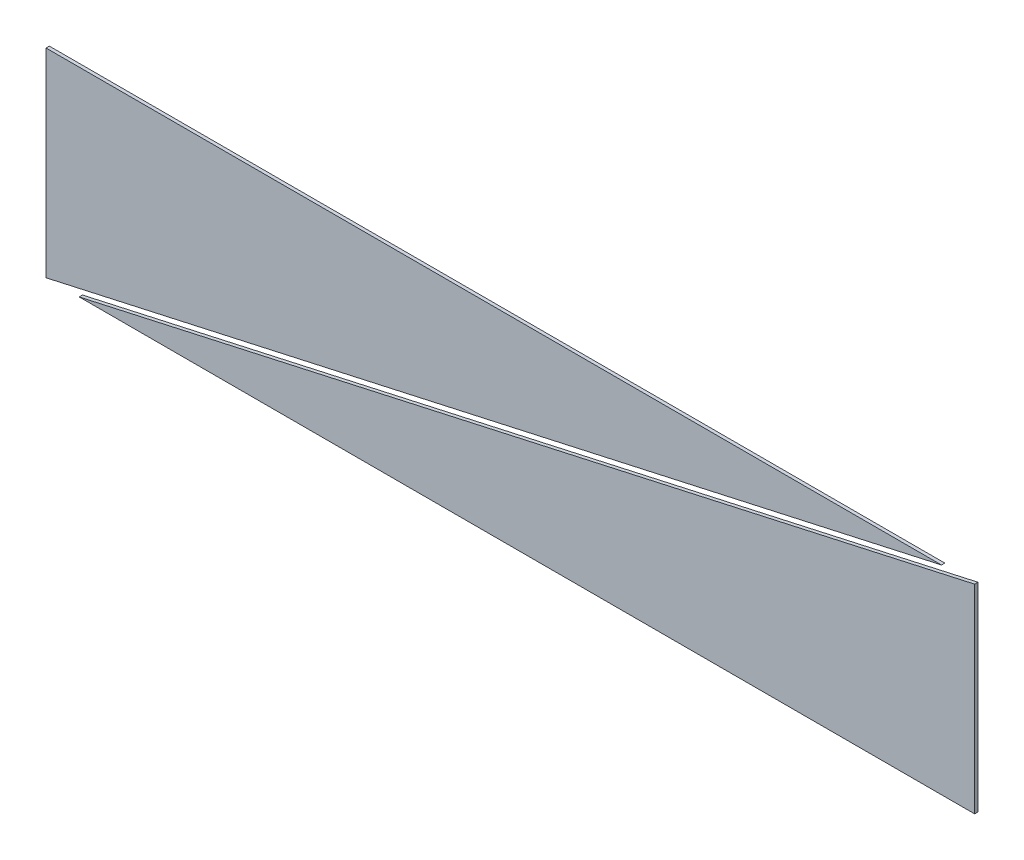
SolidWorks part; units mm, degrees
ref_plane "Front Plane" through (0, 0, 0) normal (0, 0, 1) x (1, 0, 0)
ref_plane "Top Plane" through (0, 0, 0) normal (0, 1, 0) x (1, 0, 0)
ref_plane "Right Plane" through (0, 0, 0) normal (1, 0, 0) x (0, 0, -1)
sketch "Sketch11" plane through (0, -5, 0) normal (0, 0, 1) x (1, 0, 0)
  line L0 (-35, 12.5) -> (32.5, 12.5)
  line L1 (-35, 12.5) -> (-35, -2.5)
  line L2 (-32.5, -2.5) -> (35, -2.5)
  line L3 (35, -2.5) -> (35, 12.5)
  line L5 (32.5, 12.5) -> (-35, -2.5)
  line L6 (35, 12.5) -> (-32.5, -2.5)
extrude "Boss-Extrude1" add sketch "Sketch11" along normal blind 0.25
